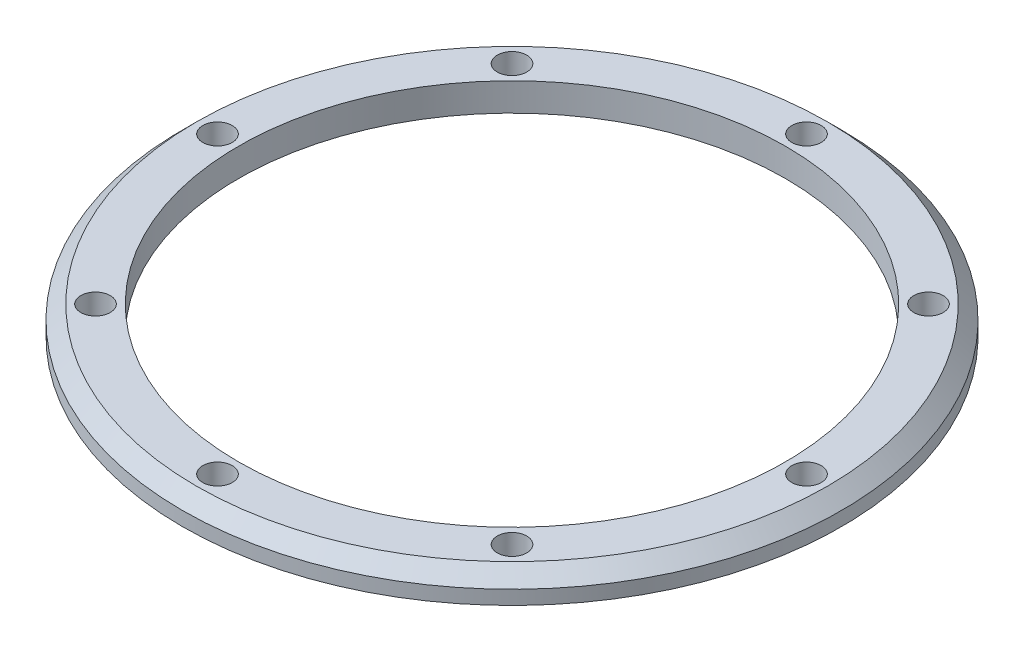
SolidWorks part; units mm, degrees
material "6061-T6 (SS)"
ref_plane "前视基准面" through (0, 0, 0) normal (0, 0, 1) x (1, 0, 0)
ref_plane "上视基准面" through (0, 0, 0) normal (0, 1, 0) x (1, 0, 0)
ref_plane "右视基准面" through (0, 0, 0) normal (1, 0, 0) x (0, 0, -1)
sketch "草图1" plane through (0, 0, 0) normal (0, 0, 1) x (1, 0, 0)
  line L0 (0, 0) -> (0, 24.7963) construction
  line L1 (-39, 0) -> (-47, 0)
  line L2 (-47, 0) -> (-47, 2)
  line L3 (-45, 4) -> (-39, 4)
  line L4 (-39, 4) -> (-39, 0)
  line L6 (-45, 4) -> (-47, 2)
  dimension "D1" = 94
  dimension "D2" = 78
  dimension "D3" = 4
  dimension "D5" = 6
  dimension "D6" = 45
revolve "旋转1" add sketch "草图1" angle 360 about L0
sketch "草图2" plane through (0, 0, 0) normal (0, -1, 0) x (1, 0, 0)
  circle A0 centre (0, 0) radius 42 construction
  circle A1 centre (0, 42) radius 2.1
  circle A2 centre (29.6985, 29.6985) radius 2.1
  circle A3 centre (42, 0) radius 2.1
  circle A4 centre (29.6985, -29.6985) radius 2.1
  circle A5 centre (0, -42) radius 2.1
  circle A6 centre (-29.6985, -29.6985) radius 2.1
  circle A7 centre (-42, 0) radius 2.1
  circle A8 centre (-29.6985, 29.6985) radius 2.1
  point P22 (0, 0)
  dimension "D1" = 84
  dimension "D2" = 4.2
  dimension "D3" = 8
extrude "切除-拉伸1" cut sketch "草图2" against normal blind 10
